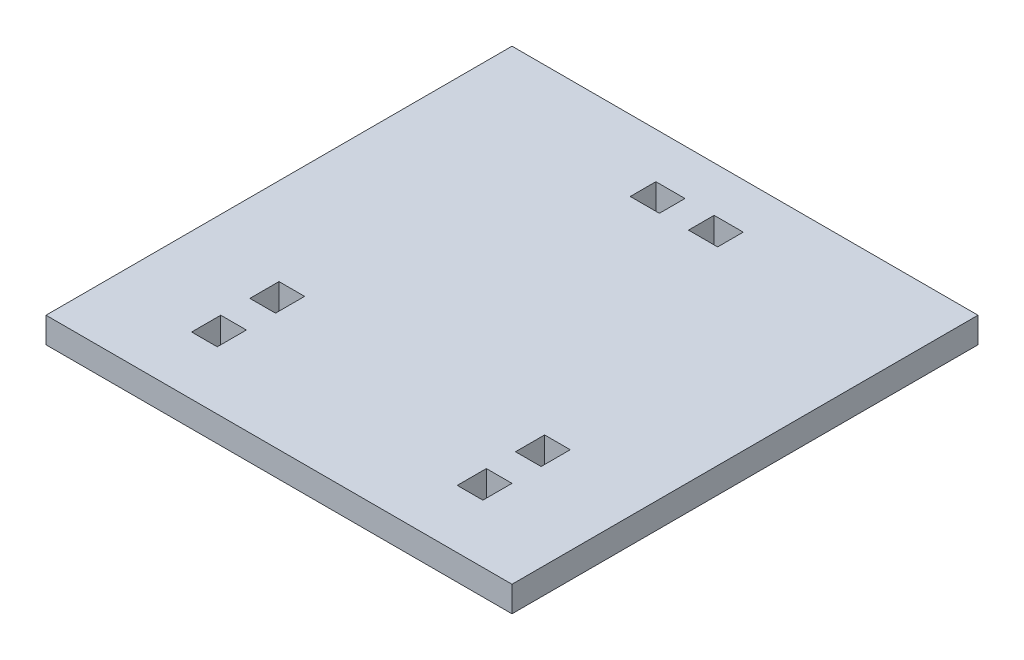
SolidWorks part; units mm, degrees
ref_plane "Front Plane" through (0, 0, 0) normal (0, 0, 1) x (1, 0, 0)
ref_plane "Top Plane" through (0, 0, 0) normal (0, 1, 0) x (1, 0, 0)
ref_plane "Right Plane" through (0, 0, 0) normal (1, 0, 0) x (0, 0, -1)
sketch "Sketch1" plane through (0, 0, 0) normal (0, 1, 0) x (1, 0, 0)
  line L0 (50.8, 101.6) -> (50.8, 0) construction
  line L1 (0, 0) -> (101.6, 0)
  line L2 (0, 0) -> (0, 101.6)
  line L3 (0, 101.6) -> (101.6, 101.6)
  line L4 (101.6, 0) -> (101.6, 101.6)
  line L5 (21.844, 101.6) -> (21.844, 0) construction
  line L6 (76.962, 19.05) -> (76.962, 12.7)
  line L7 (19.05, 31.75) -> (24.638, 31.75)
  line L8 (19.05, 31.75) -> (19.05, 25.4)
  line L9 (19.05, 25.4) -> (24.638, 25.4)
  line L10 (24.638, 31.75) -> (24.638, 25.4)
  line L11 (19.05, 19.05) -> (24.638, 19.05)
  line L12 (19.05, 19.05) -> (19.05, 12.7)
  line L13 (19.05, 12.7) -> (24.638, 12.7)
  line L14 (24.638, 19.05) -> (24.638, 12.7)
  line L15 (82.55, 12.7) -> (76.962, 12.7)
  line L16 (82.55, 19.05) -> (82.55, 12.7)
  line L17 (82.55, 19.05) -> (76.962, 19.05)
  line L18 (82.55, 31.75) -> (82.55, 25.4)
  line L19 (76.962, 31.75) -> (76.962, 25.4)
  line L20 (82.55, 25.4) -> (76.962, 25.4)
  line L21 (82.55, 31.75) -> (76.962, 31.75)
  line L22 (0, 88.9) -> (101.6, 88.9) construction
  line L23 (47.625, 88.9) -> (53.975, 88.9) construction
  line L24 (41.275, 86.106) -> (47.625, 86.106)
  line L25 (41.275, 86.106) -> (41.275, 91.694)
  line L26 (41.275, 91.694) -> (47.625, 91.694)
  line L27 (47.625, 86.106) -> (47.625, 91.694)
  line L28 (53.975, 86.106) -> (60.325, 86.106)
  line L29 (53.975, 86.106) -> (53.975, 91.694)
  line L30 (53.975, 91.694) -> (60.325, 91.694)
  line L31 (60.325, 86.106) -> (60.325, 91.694)
  point P17 (21.844, 31.75)
  point P18 (21.844, 19.05)
  point P39 (50.8, 88.9)
  point P40 (50.8, 88.9)
  point P41 (19.05, 28.575)
  dimension "D1" = 101.6
  dimension "D2" = 101.6
  dimension "D3" = 6.35
  dimension "D4" = 5.588
  dimension "D5" = 6.35
  dimension "D6" = 31.75
  dimension "D7" = 12.7
  dimension "D8" = 12.7
  dimension "D9" = 6.35
  dimension "D10" = 6.35
  dimension "D11" = 5.588
extrude "Boss-Extrude1" add sketch "Sketch1" along normal blind 5.588
